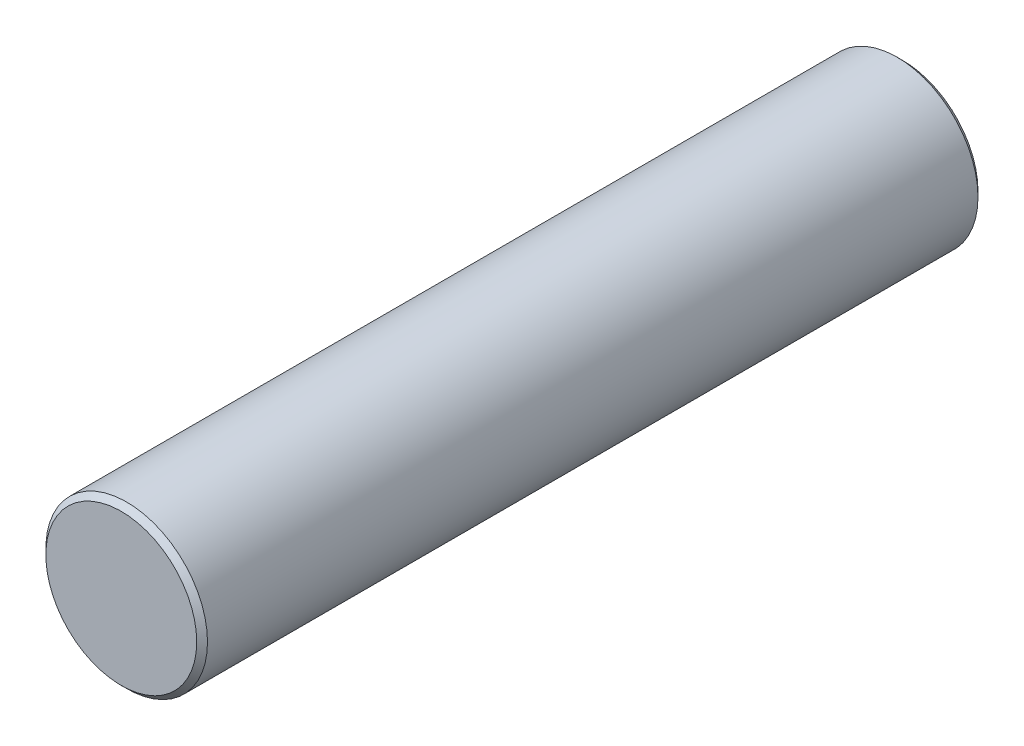
SolidWorks part; units mm, degrees
ref_plane "Front Plane" through (0, 0, 0) normal (0, 0, 1) x (1, 0, 0)
ref_plane "Top Plane" through (0, 0, 0) normal (0, 1, 0) x (1, 0, 0)
ref_plane "Right Plane" through (0, 0, 0) normal (1, 0, 0) x (0, 0, -1)
sketch "Sketch1" plane through (0, 0, 0) normal (0, 0, 1) x (1, 0, 0)
  circle A0 centre (0, 0) radius 0.75
  dimension "D1" = 1.5
extrude "Boss-Extrude1" add sketch "Sketch1" along normal blind 7.25
chamfer "Chamfer1" distance 0.05 angle 45 2 edges at (0.75, 0, 0) (0.75, 0, 7.25)
